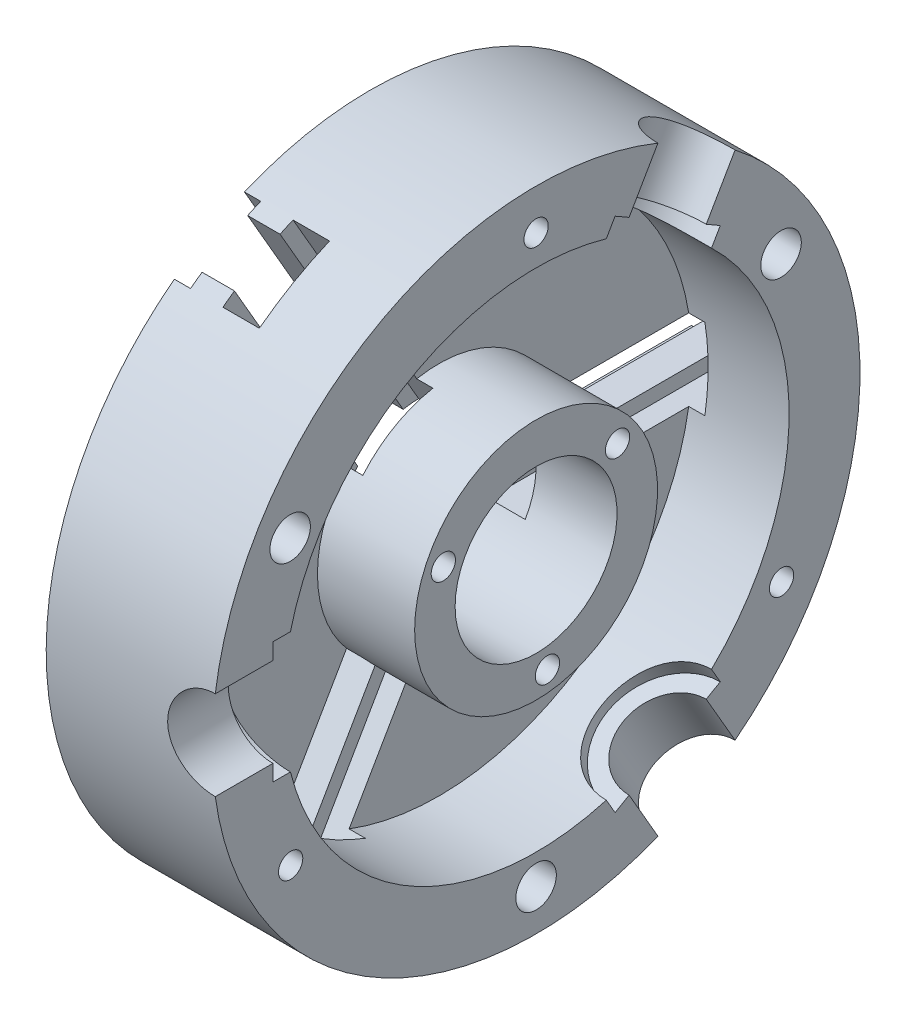
SolidWorks part; units mm, degrees
ref_plane "Front Plane" through (0, 0, 0) normal (0, 0, 1) x (1, 0, 0)
ref_plane "Top Plane" through (0, 0, 0) normal (0, 1, 0) x (1, 0, 0)
ref_plane "Right Plane" through (0, 0, 0) normal (1, 0, 0) x (0, 0, -1)
sketch "Sketch1" plane through (0, 0, 0) normal (0, 0, 1) x (1, 0, 0)
  line L0 (0, 20) -> (0, 80)
  line L1 (0, 80) -> (41, 80)
  line L2 (41, 80) -> (41, 62.5)
  line L3 (41, 62.5) -> (17, 62.5)
  line L4 (17, 62.5) -> (17, 30)
  line L5 (17, 30) -> (41, 30)
  line L6 (41, 30) -> (41, 20)
  line L7 (41, 20) -> (0, 20)
  line L8 (-1000, 0) -> (49000, 0) construction
  dimension "D1" = 80
  dimension "D2" = 41
  dimension "D3" = 60
  dimension "D4" = 24
  dimension "D5" = 20
  dimension "D6" = 62.5
  dimension "D7" = 30
revolve "Revolve1" add sketch "Sketch1" angle 360 about L8
sketch "Sketch3" plane through (0, 0, 0) normal (0, 0, 1) x (1, 0, 0)
  line L0 (0, -10) -> (0, 10)
  line L1 (0, 80) -> (0, -80) construction
  line L2 (0, 10) -> (4, 10)
  line L3 (4, 10) -> (4, 6.5)
  line L4 (4, 6.5) -> (12, 6.5)
  line L5 (12, 6.5) -> (12, 10)
  line L6 (12, 10) -> (21, 10)
  line L7 (21, 10) -> (21, -10)
  line L9 (12, -10) -> (21, -10)
  line L10 (12, -6.5) -> (12, -10)
  line L11 (4, -10) -> (4, -6.5)
  line L12 (0, -10) -> (4, -10)
  line L13 (4, -6.5) -> (12, -6.5)
  dimension "D2" = 4
extrude "Cut-Extrude1" cut sketch "Sketch3" against normal through all
pattern_circular "CirPattern1" count 3 over 360 about axis through (0, 0, 0) along (1, 0, 0) of "Cut-Extrude1"
sketch "Sketch5" plane through (0, 0, 0) normal (-1, 0, 0) x (0, 0, 1)
  line L0 (0, 0) -> (25000, -43301.2702) construction
  line L1 (0, 0) -> (0, -50000) construction
  arc A0 (31.026, -73.7386) -> (48.3465, -63.7386) centre (0, 0) ccw construction
  circle A1 centre (0, 0) radius 69.8611 construction
  circle A2 centre (0, -69.8611) radius 5
  circle A3 centre (-60.5016, 35.2082) radius 5
  circle A4 centre (60.7419, 35.0695) radius 5
  point P6 (40, -69.282)
  point P21 (0.0801, 0.1389)
  dimension "D2" = 3
  dimension "D1" = 30
extrude "Cut-Extrude2" cut sketch "Sketch5" against normal blind 30 from offset 11 offset against normal yes
sketch "Sketch6" plane through (0, 0, 0) normal (-1, 0, 0) x (0, 0, 1)
  line L0 (0, 0) -> (25000, -43301.2702) construction
  line L1 (0, 0) -> (0, 50000) construction
  circle A0 centre (0, 0) radius 70 construction
  arc A1 (31.026, -73.7386) -> (48.3465, -63.7386) centre (0, 0) ccw construction
  point P79 (40, -69.282)
  dimension "D1" = 30
sketch "Sketch9" plane through (0, 0, 0) normal (-1, 0, 0) x (0, 0, 1)
  line L0 (-100000, 173205.0808) -> (125000, -216506.3509) construction
  circle A0 centre (0, 0) radius 25 construction
  circle A1 centre (-20.1167, 14.8431) radius 3
  dimension "D1" = 50
  dimension "D2" = 10
extrude "Cut-Extrude3" cut sketch "Sketch9" against normal up to next (41 mm away)
pattern_circular "CirPattern3" count 3 over 360 about axis through (0, 0, 0) along (1, 0, 0) of "Cut-Extrude3"
ref_plane "Plane2" through (0, 0, 80) normal (0, 0, 1) x (1, 0, 0)
sketch "Sketch11" plane through (0, 0, 80) normal (0, 0, 1) x (1, 0, 0)
  line L0 (41, -80) -> (41, 80) construction
  circle A0 centre (41, 0) radius 11
extrude "Cut-Extrude4" cut sketch "Sketch11" against normal blind 15
sketch "Sketch12" plane through (0, 0, 65) normal (0, 0, 1) x (1, 0, 0)
  line L0 (41, -11) -> (41, 11) construction
  circle A0 centre (41, 0) radius 15
extrude "Cut-Extrude5" cut sketch "Sketch12" against normal up to next
sketch "Sketch15" plane through (11, 0, 0) normal (1, 0, 0) x (0, 0, -1)
  line L1 (-5, -78.3611) -> (5, -78.3611)
  line L2 (-5, -78.3611) -> (-5, -61.3611)
  line L3 (-5, -61.3611) -> (5, -61.3611)
  line L4 (5, -78.3611) -> (5, -61.3611)
  line L5 (-5, -78.3611) -> (5, -61.3611) construction
  line L6 (-5, -61.3611) -> (5, -78.3611) construction
  point P0 (0, -69.8611)
  dimension "D1" = 17
  dimension "D2" = 10
extrude "Cut-Extrude9" cut sketch "Sketch15" against normal blind 15
pattern_circular "CirPattern5" count 3 over 360 about axis through (0, 0, 0) along (1, 0, 0) of "Cut-Extrude9"
hole_wizard "Ø6.0mm Dowel Hole3" positions "Sketch18" profile "Sketch19" hole size "Ø6.0" standard "ANSI Metric"
sketch "Sketch18" plane through (41, 0, 0) normal (1, 0, 0) x (0, 0, -1)
  line L0 (0, -200000) -> (0, 250000) construction
  circle A0 centre (0, 0) radius 70 construction
  point P0 (0, 70)
sketch "Sketch19" plane through (41, 70, 0) normal (0, 1, 0) x (0, 0, -1)
  line L0 (0, 0) -> (0, 31.8026)
  line L1 (0, 31.8026) -> (3, 30)
  line L2 (3, 30) -> (3, 0)
  line L5 (3, 0) -> (0, 0)
  line L10 (0, 31.8026) -> (-3, 30) construction
  line L11 (0, -6.35) -> (0, 107.95) construction
  dimension "Hole Dia." = 6
  dimension "Hole Depth" = 30
  dimension "Drill Angle" = 118
pattern_circular "CirPattern7" count 3 over 360 about axis through (0, 0, 0) along (1, 0, 0) of "Ø6.0mm Dowel Hole3"
pattern_circular "CirPattern8" count 3 over 360 about axis through (0, 0, 0) along (1, 0, 0) of "Cut-Extrude4", "Cut-Extrude5"
